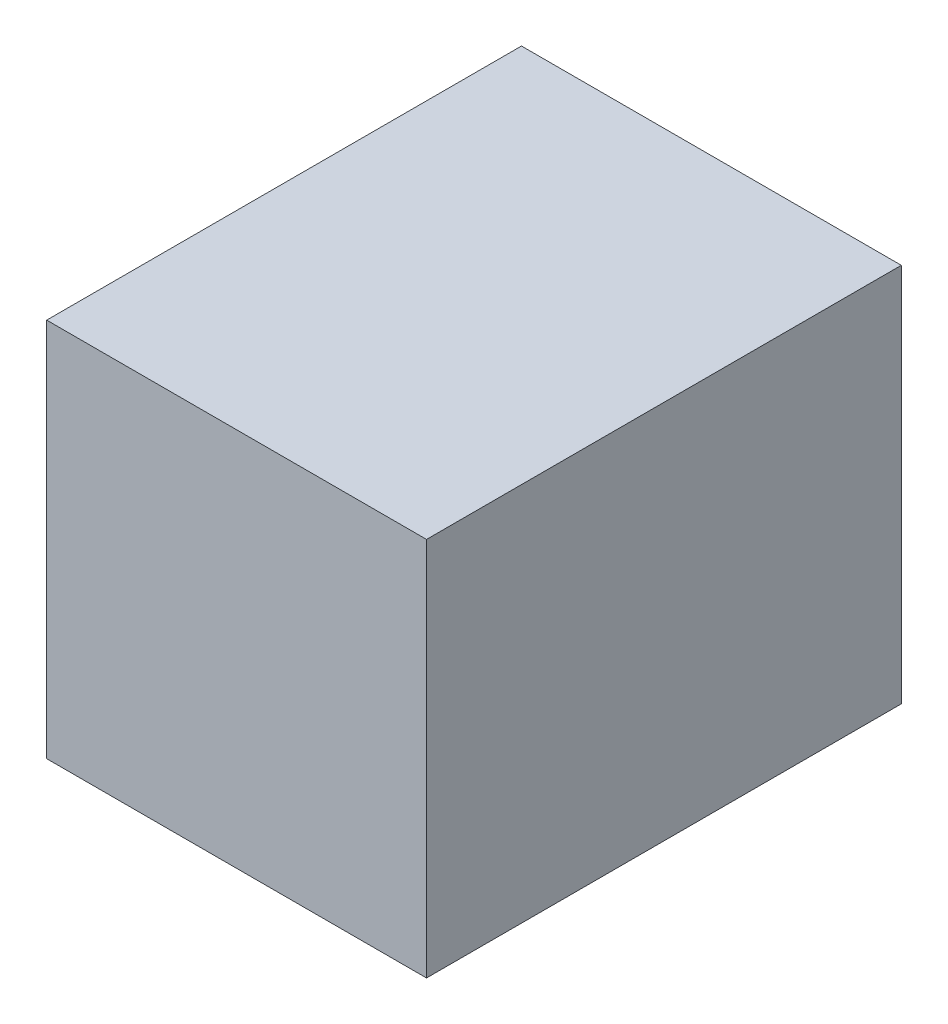
SolidWorks part; units mm, degrees
ref_plane "Front Plane" through (0, 0, 0) normal (0, 0, 1) x (1, 0, 0)
ref_plane "Top Plane" through (0, 0, 0) normal (0, 1, 0) x (1, 0, 0)
ref_plane "Right Plane" through (0, 0, 0) normal (1, 0, 0) x (0, 0, -1)
sketch "Sketch2" plane through (0, 0, 0) normal (0, 0, 1) x (1, 0, 0)
  line L1 (-8, 8) -> (8, 8)
  line L2 (-8, 8) -> (-8, -8)
  line L3 (-8, -8) -> (8, -8)
  line L4 (8, 8) -> (8, -8)
  line L5 (-8, 8) -> (8, -8) construction
  line L6 (-8, -8) -> (8, 8) construction
  point P0 (0, 0)
extrude "Boss-Extrude1" add sketch "Sketch2" along normal blind 20
sketch "Sketch3" plane through (-8, 0, 0) normal (-1, 0, 0) x (0, 0, 1)
  line L0 (0, 0) -> (20, 0) construction
  line L1 (0, 8) -> (0, -8) construction
  line L2 (20, 8) -> (20, -8) construction
  line L5 (10, 8) -> (10, -8) construction
  line L6 (20, 8) -> (0, 8) construction
  line L7 (20, -8) -> (0, -8) construction
  circle A0 centre (10, 0) radius 2
extrude "Boss-Extrude2" add sketch "Sketch3" along normal blind 6
